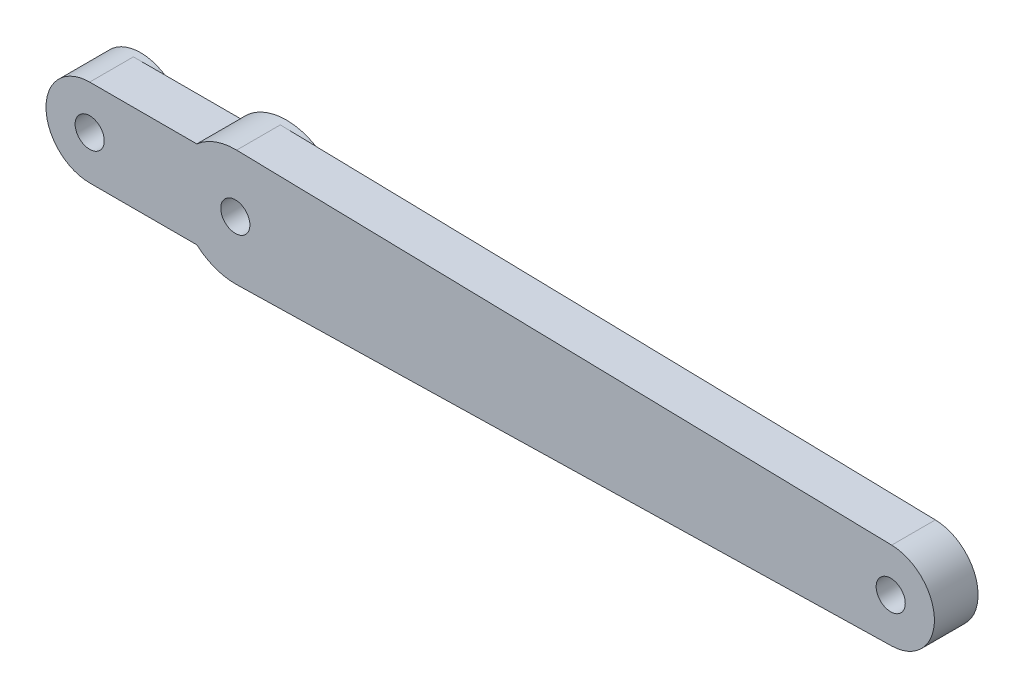
SolidWorks part; units mm, degrees
ref_plane "Front Plane" through (0, 0, 0) normal (0, 0, 1) x (1, 0, 0)
ref_plane "Top Plane" through (0, 0, 0) normal (0, 1, 0) x (1, 0, 0)
ref_plane "Right Plane" through (0, 0, 0) normal (1, 0, 0) x (0, 0, -1)
sketch "Sketch1" plane through (0, 0, 0) normal (0, 0, 1) x (1, 0, 0)
  line L0 (0, 0) -> (-10, 0) construction
  line L1 (0, -3) -> (-10, -3)
  line L2 (0, 3) -> (-10, 3)
  line L3 (0.0889, -3.999) -> (45.0667, -2.9993)
  line L4 (0.0889, 3.999) -> (45.0667, 2.9993)
  circle A0 centre (0, 0) radius 1
  circle A1 centre (45, 0) radius 1
  circle A2 centre (-10, 0) radius 1
  circle A3 centre (0, 0) radius 4
  circle A4 centre (45, 0) radius 3
  arc A5 (0, -3) -> (0, 3) centre (0, 0) ccw
  arc A6 (-10, 3) -> (-10, -3) centre (-10, 0) ccw
  point P9 (-5, 0)
  dimension "D2" = 2
  dimension "D4" = 8
  dimension "D5" = 6
  dimension "D6" = 3
  dimension "D1" = 45
  dimension "D3" = 10
extrude "Boss-Extrude1" add sketch "Sketch1" along normal blind 3
sketch "Sketch2" plane through (0, 0, 0) normal (0, 0, -1) x (-1, 0, 0)
  circle A0 centre (10, 0) radius 3
  circle A1 centre (0, 0) radius 4
  circle A2 centre (0, 0) radius 1 construction
  circle A3 centre (0, 0) radius 1
  circle A4 centre (10, 0) radius 1 construction
  circle A5 centre (10, 0) radius 1
  arc A6 (2.6458, 3) -> (-0.0889, 3.999) centre (0, 0) ccw construction
  point P6 (-8.9254, -4.5098)
  point P15 (0, 0)
  point P16 (9.5398, 0)
extrude "Boss-Extrude2" add sketch "Sketch2" along normal blind 0.5
